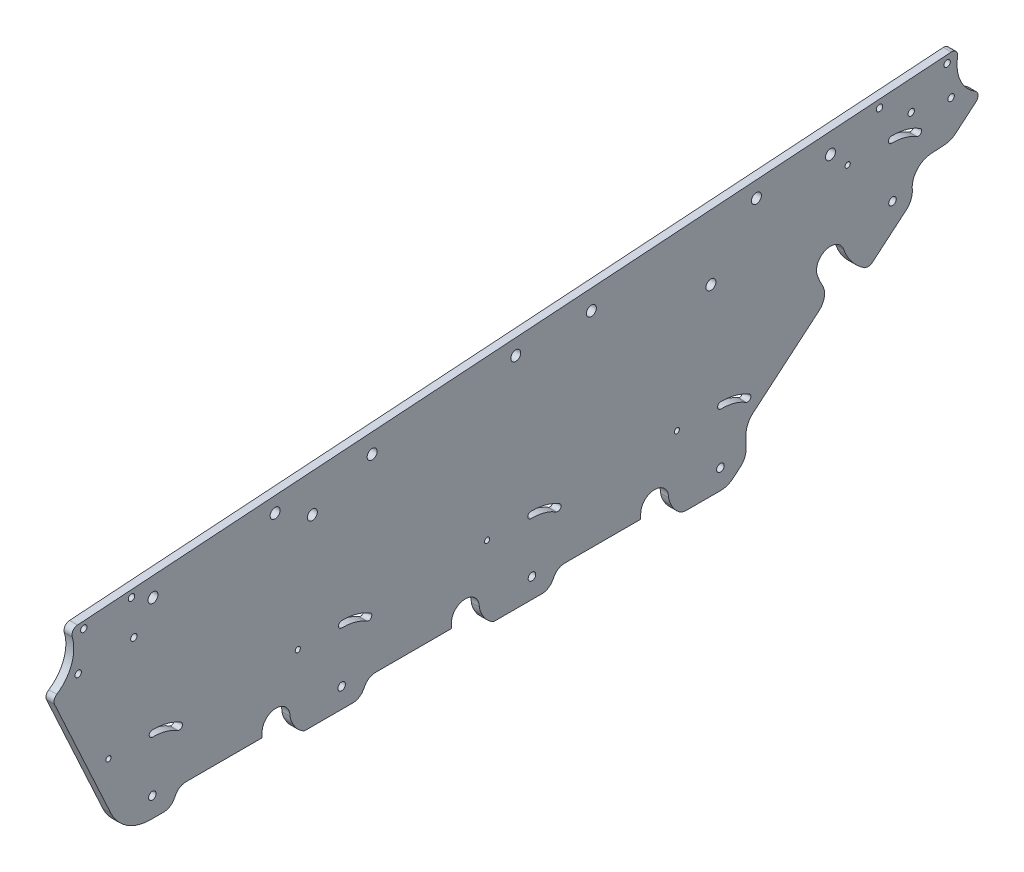
SolidWorks part; units mm, degrees
ref_plane "前视基准面" through (0, 0, 0) normal (0, 0, 1) x (1, 0, 0)
ref_plane "上视基准面" through (0, 0, 0) normal (0, 1, 0) x (1, 0, 0)
ref_plane "右视基准面" through (0, 0, 0) normal (1, 0, 0) x (0, 0, -1)
sketch "草图1" plane through (0, 0, 0) normal (-1, 0, 0) x (0, 0, 1)
  line L0 (79.9418, 312.7793) -> (79.9418, 310.3794)
  line L1 (-15.0582, 312.7793) -> (-15.0582, 310.3548)
  line L2 (-262.4713, 396.8637) -> (-255.6293, 396.4086)
  line L3 (-110.0582, 312.7793) -> (-110.0582, 310.3752)
  line L4 (-162.9047, 314.2174) -> (-162.9047, 320.7531)
  line L5 (-278.2528, 407.6106) -> (-268.2462, 399.1902)
  line L8 (-225.9662, 363.5596) -> (-242.7807, 377.7089)
  line L9 (-199.49, 356.194) -> (-166.4661, 328.4045)
  line L12 (79.9418, 310.3794) -> (118.0488, 310.3794)
  line L13 (-15.0582, 310.3548) -> (23.0756, 310.3548)
  line L14 (-110.0582, 310.3752) -> (-71.8978, 310.3752)
  line L42 (129.3553, 302.7793) -> (135.8467, 302.7793)
  line L53 (34.3713, 302.7793) -> (58.6944, 302.7793)
  line L54 (-60.5308, 302.7793) -> (-36.3056, 302.7793)
  line L62 (-265.9135, 435.515) -> (172.5491, 405.7332)
  line L63 (155.833, 315.5843) -> (184.1003, 377.0265)
  line L65 (-156.5281, 305.1279) -> (-160.0556, 308.0962)
  line L68 (-150.0895, 302.7793) -> (-132.9628, 302.7793)
  circle A0 centre (134.6976, 398.7144) radius 2.5
  circle A1 centre (-205.3024, 421.3291) radius 2.5
  circle A3 centre (24.6976, 406.0309) radius 2.5
  arc A4 (-156.5281, 305.1279) -> (-150.0895, 302.7793) centre (-150.0895, 312.7793) ccw
  arc A5 (135.8467, 302.7793) -> (155.833, 315.5843) centre (135.8467, 324.7793) ccw
  circle A6 centre (54.6976, 394.7144) radius 2.5
  arc A7 (-66.5574, 307.1102) -> (-65.2315, 305.0506) centre (-55.4881, 312.7793) ccw
  circle A8 centre (-145.3024, 394.7144) radius 2.5
  circle A10 centre (-85.3024, 413.3475) radius 2.5
  arc A11 (28.4469, 307.0285) -> (29.4805, 305.3037) centre (40, 312.7793) ccw
  arc A12 (123.4249, 307.0434) -> (124.4598, 305.3102) centre (135, 312.7793) ccw
  arc A13 (123.4249, 307.0434) -> (118.0488, 310.3794) centre (118.0488, 304.3794) ccw
  arc A14 (23.0756, 310.3548) -> (28.4469, 307.0285) centre (23.0756, 304.3548) cw
  arc A15 (-71.8978, 310.3752) -> (-66.5574, 307.1102) centre (-71.8978, 304.3752) cw
  circle A18 centre (-229.9125, 429.2269) radius 1.6
  circle A19 centre (-263.8307, 431.5848) radius 1.6
  circle A21 centre (-245.8276, 419.3316) radius 1.6
  arc A22 (-129.3492, 303.9896) -> (-132.9628, 302.7793) centre (-132.9628, 308.7793) cw
  arc A23 (34.3713, 302.7793) -> (29.4805, 305.3037) centre (34.3713, 308.7793) cw
  circle A24 centre (-213.9248, 412.4193) radius 1.3
  arc A25 (-60.5308, 302.7793) -> (-65.2315, 305.0506) centre (-60.5308, 308.7793) cw
  arc A26 (-205.3024, 374.4129) -> (-218.7886, 357.5197) centre (-236.4128, 385.4193) cw construction
  arc A27 (-199.49, 356.194) -> (-201.3514, 366.1658) centre (-194.3391, 362.3151) cw
  arc A28 (-222.5271, 363.4378) -> (-225.9662, 363.5596) centre (-224.1031, 367.5509) cw
  arc A29 (-222.5271, 363.4378) -> (-211.9016, 376.7476) centre (-236.4128, 385.4193) ccw
  arc A30 (129.3553, 302.7793) -> (124.4598, 305.3102) centre (129.3553, 308.7793) cw
  arc A31 (-166.4661, 328.4045) -> (-162.9047, 320.7531) centre (-172.9047, 320.7531) cw
  arc A32 (-262.4713, 396.8637) -> (-268.2462, 399.1902) centre (-261.8076, 406.8416) cw
  arc A33 (-255.6293, 396.4086) -> (-246.3447, 385.4148) centre (-256.293, 386.4306) cw
  arc A34 (-246.3447, 385.4148) -> (-242.7807, 377.7089) centre (-237.5156, 384.8212) ccw
  arc A35 (-162.9047, 314.2174) -> (-160.0556, 308.0962) centre (-154.9047, 314.2174) ccw
  arc A36 (-198.7032, 372.0782) -> (-211.9016, 376.7476) centre (-205.3024, 374.4129) ccw
  arc A37 (-201.3514, 366.1658) -> (-198.7032, 372.0782) centre (-236.4128, 385.4193) ccw
  arc A38 (184.1003, 377.0265) -> (182.9947, 380.8056) centre (181.3749, 378.2804) ccw
  arc A39 (172.5491, 405.7332) -> (175.2178, 401.873) centre (172.3458, 402.7401) cw
  arc A40 (-278.2528, 407.6106) -> (-277.8828, 412.4676) centre (-276.3212, 409.9061) cw
  arc A41 (-265.9135, 435.515) -> (-269.0706, 431.9978) centre (-266.1168, 432.5219) ccw
  arc A42 (-235.9248, 412.4193) -> (-249.4461, 408.7897) centre (-236.4128, 387.2375) ccw construction
  arc A43 (-235.8937, 414.019) -> (-250.274, 410.1588) centre (-236.4128, 387.2375) ccw
  arc A44 (-235.9558, 410.8196) -> (-248.6181, 407.4205) centre (-236.4128, 387.2375) ccw
  arc A45 (-235.9558, 410.8196) -> (-235.8937, 414.019) centre (-235.9248, 412.4193) ccw
  arc A46 (-250.274, 410.1588) -> (-248.6181, 407.4205) centre (-249.4461, 408.7897) ccw
  circle A47 centre (-265.8276, 415.7099) radius 1.6
  circle A48 centre (145.4523, 404.1659) radius 1.6
  circle A50 centre (172.2236, 384.3846) radius 1.6
  circle A51 centre (169.3971, 402.5395) radius 1.6
  circle A52 centre (144.2828, 386.2039) radius 1.6
  circle A132 centre (-236.4128, 385.4193) radius 1.9
  circle A133 centre (-128.2113, 339.7793) radius 1.3
  arc A138 (-125.8547, 308.0793) -> (-129.3492, 303.9896) centre (-136.8604, 313.9454) cw
  circle A140 centre (62, 339.7793) radius 1.3
  circle A144 centre (40, 312.7793) radius 1.9
  arc A150 (64.1453, 308.0793) -> (65.9418, 312.7793) centre (54.0836, 314.6186) ccw
  circle A156 centre (-47.3651, 412.8285) radius 2.5
  arc A157 (-110.0582, 312.7793) -> (-124.0582, 312.7793) centre (-117.0582, 312.7793) ccw
  arc A162 (-30.8547, 308.0793) -> (-29.0582, 312.7793) centre (-40.9164, 314.6186) ccw
  circle A173 centre (-55.4881, 312.7793) radius 1.9
  circle A174 centre (-33, 339.7793) radius 1.3
  arc A179 (-30.8547, 308.0793) -> (-36.3056, 302.7793) centre (-41.8604, 313.9454) cw
  circle A185 centre (-168.1302, 420.8611) radius 2.5
  circle A186 centre (73.3999, 404.796) radius 2.5
  arc A191 (64.1453, 308.0793) -> (58.6944, 302.7793) centre (53.1396, 313.9454) cw
  arc A196 (79.9418, 312.7793) -> (65.9418, 312.7793) centre (72.9418, 312.7793) ccw
  arc A197 (-125.8547, 308.0793) -> (-124.0582, 312.7793) centre (-135.9164, 314.6186) ccw
  circle A198 centre (157, 339.7793) radius 1.3
  arc A201 (-117.0582, 312.7793) -> (-121.1229, 302.7793) centre (-135.9164, 314.6186) cw construction
  circle A202 centre (-150.0582, 312.7793) radius 1.9
  arc A208 (-277.8828, 412.4676) -> (-269.0706, 431.9978) centre (-287.7673, 428.6807) ccw
  circle A214 centre (135, 312.7793) radius 1.9
  arc A220 (175.2178, 401.873) -> (182.9947, 380.8056) centre (193.0538, 396.4879) ccw
  arc A221 (-15.0582, 312.7793) -> (-29.0582, 312.7793) centre (-22.0582, 312.7793) ccw
  arc A226 (-55, 339.7793) -> (-68.5213, 336.1497) centre (-55.4881, 314.5975) ccw construction
  arc A227 (-54.969, 341.379) -> (-69.3493, 337.5188) centre (-55.4881, 314.5975) ccw
  arc A228 (-55.031, 338.1796) -> (-67.6934, 334.7805) centre (-55.4881, 314.5975) ccw
  arc A229 (-55.031, 338.1796) -> (-54.969, 341.379) centre (-55, 339.7793) ccw
  arc A230 (-69.3493, 337.5188) -> (-67.6934, 334.7805) centre (-68.5213, 336.1497) ccw
  arc A231 (-150.2113, 339.7793) -> (-163.7326, 336.1497) centre (-150.6994, 314.5975) ccw construction
  arc A232 (-150.1803, 341.379) -> (-164.5606, 337.5188) centre (-150.6994, 314.5975) ccw
  arc A233 (-150.2423, 338.1796) -> (-162.9047, 334.7805) centre (-150.6994, 314.5975) ccw
  arc A234 (-150.2423, 338.1796) -> (-150.1803, 341.379) centre (-150.2113, 339.7793) ccw
  arc A235 (-164.5606, 337.5188) -> (-162.9047, 334.7805) centre (-163.7326, 336.1497) ccw
  arc A241 (40, 339.7793) -> (26.4787, 336.1497) centre (39.5119, 314.5975) ccw construction
  arc A242 (40.031, 341.379) -> (25.6507, 337.5188) centre (39.5119, 314.5975) ccw
  arc A243 (39.969, 338.1796) -> (27.3066, 334.7805) centre (39.5119, 314.5975) ccw
  arc A244 (39.969, 338.1796) -> (40.031, 341.379) centre (40, 339.7793) ccw
  arc A245 (25.6507, 337.5188) -> (27.3066, 334.7805) centre (26.4787, 336.1497) ccw
  arc A246 (135, 339.7793) -> (121.4787, 336.1497) centre (134.5119, 314.5975) ccw construction
  arc A247 (135.031, 341.379) -> (120.6507, 337.5188) centre (134.5119, 314.5975) ccw
  arc A248 (134.969, 338.1796) -> (122.3066, 334.7805) centre (134.5119, 314.5975) ccw
  arc A249 (134.969, 338.1796) -> (135.031, 341.379) centre (135, 339.7793) ccw
  arc A250 (120.6507, 337.5188) -> (122.3066, 334.7805) centre (121.4787, 336.1497) ccw
  point P0 (-150, 0)
  point P1 (135, 0)
  point P9 (-344.9533, 138.7825)
  point P10 (187.1329, 101.1747)
  point P11 (165.9429, -19)
  point P12 (-156.9154, -19)
  point P67 (-210.6231, 364.8307)
  point P72 (-211.6166, 365.2818)
  point P90 (-265.7372, 397.0266)
  point P108 (-242.9427, 411.5628)
  point P288 (-31.725, 307.5809)
  point P313 (68.6487, 307.479)
  point P318 (-131.7259, 307.5821)
  point P340 (-62.0179, 338.9228)
  point P357 (-157.2292, 338.9228)
  point P380 (32.9821, 338.9228)
  point P392 (127.9821, 338.9228)
  dimension "D7" = 10
  dimension "D8" = 8
  dimension "D9" = 7
  dimension "D10" = 10
  dimension "D4" = 6
  dimension "D11" = 10
  dimension "D12" = 10
  dimension "D13" = 10
  dimension "D14" = 24
  dimension "D15" = 27
  dimension "D16" = 10
  dimension "D17" = 27
  dimension "D18" = 27
  dimension "D19" = 27
  dimension "D20" = 8
  dimension "D6" = 6
  dimension "D5" = 6
  dimension "D21" = 10
  dimension "D22" = 3
  dimension "D23" = 18
  dimension "D24" = 3.2
  dimension "D25" = 16
  dimension "D28" = 3.78
  dimension "D29" = 34
  dimension "D30" = 28
  dimension "D31" = 3.2
  dimension "D32" = 3.2
  dimension "D33" = 3.2
  dimension "D35" = 20
  dimension "D36" = 3.834
  dimension "D39" = 5
  dimension "D34" = 3.2
  dimension "D2" = 22
  dimension "D1" = 10
  dimension "D3" = 7
  dimension "D26" = 3.8
  dimension "D27" = 9.8953
  dimension "D37" = 3.4
  dimension "D38" = 3.4
extrude "凸台-拉伸1" add sketch "草图1" along normal blind 4
